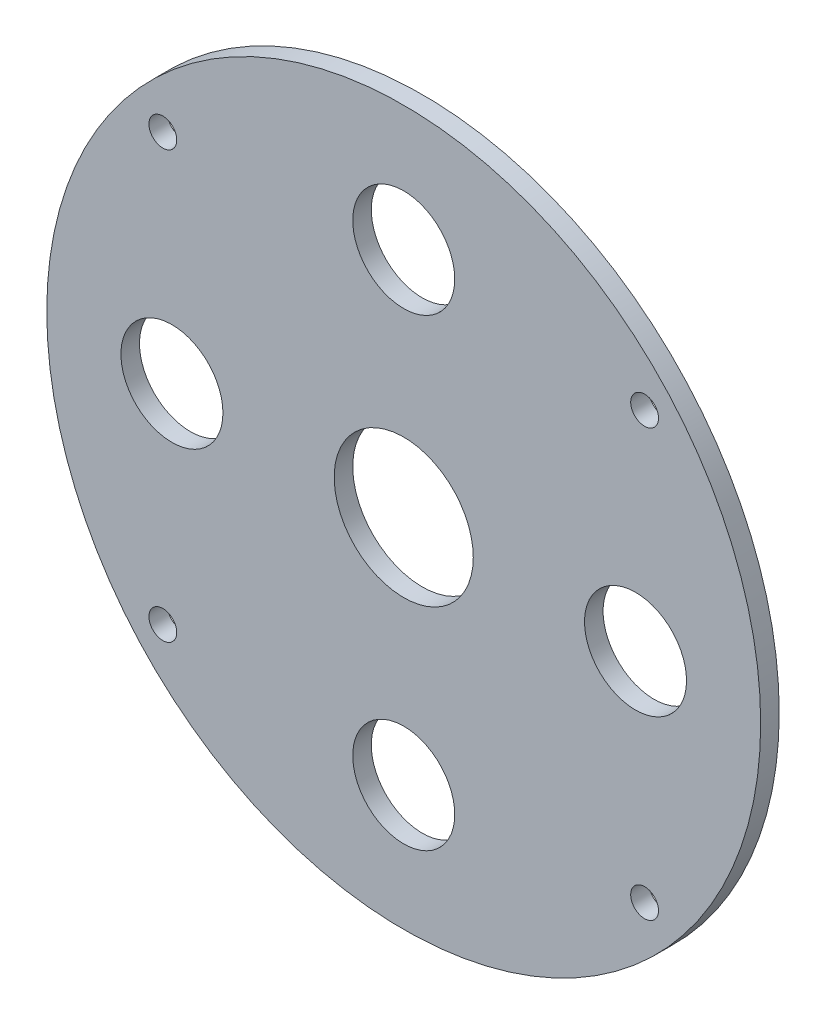
SolidWorks part; units mm, degrees
material "Acrylic (Medium-high impact)"
ref_plane "Front Plane" through (0, 0, 0) normal (0, 0, 1) x (1, 0, 0)
ref_plane "Top Plane" through (0, 0, 0) normal (0, 1, 0) x (1, 0, 0)
ref_plane "Right Plane" through (0, 0, 0) normal (1, 0, 0) x (0, 0, -1)
sketch "Model" plane through (0, 0, 0) normal (0, 0, 1) x (1, 0, 0)
  circle A0 centre (-25, 0) radius 5.5
  circle A1 centre (0, 25) radius 5.5
  circle A2 centre (0, -25) radius 5.5
  circle A3 centre (25, 0) radius 5.5
  circle A4 centre (0, 0) radius 7.5
  circle A5 centre (0, 0) radius 38.5
  circle A6 centre (25.9808, -23) radius 1.5
  circle A7 centre (-25.9808, -23) radius 1.5
  circle A34 centre (25.9808, 23) radius 1.5
  circle A35 centre (-25.9808, 23) radius 1.5
  dimension "D1" = 15
  dimension "D2" = 77
  dimension "D3" = 11
  dimension "D4" = 3
  dimension "D5" = 25
  dimension "D6" = 25.9808
  dimension "D7" = 25
  dimension "D8" = 25.9808
  dimension "D9" = 23
  dimension "D10" = 25
  dimension "D11" = 23
  dimension "D12" = 25
extrude "Boss-Extrude1" add sketch "Model" along normal blind 2
